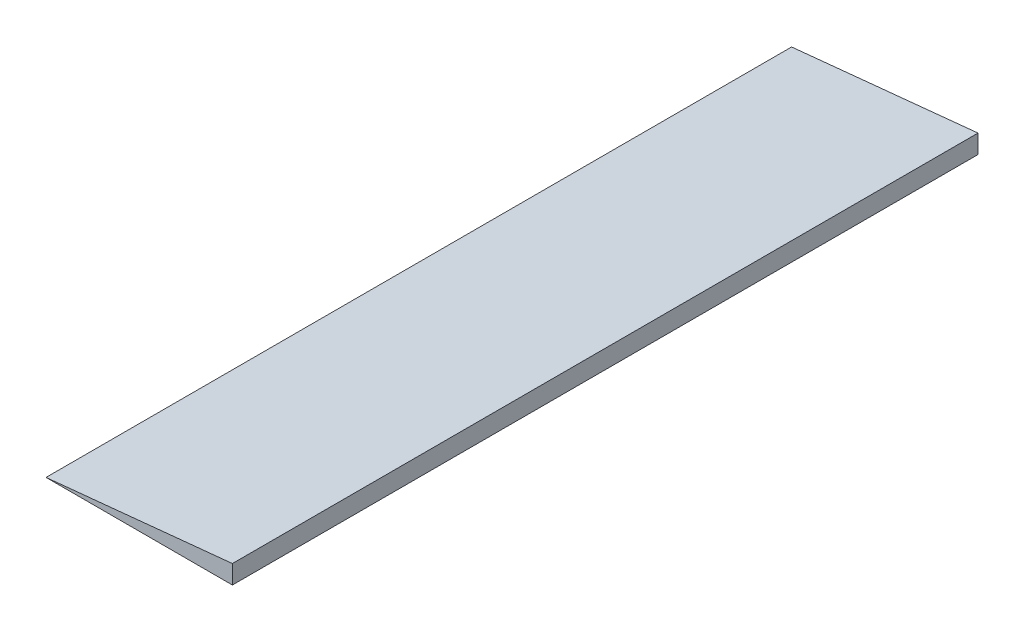
SolidWorks part; units mm, degrees
ref_plane "Front Plane" through (0, 0, 0) normal (0, 0, 1) x (1, 0, 0)
ref_plane "Top Plane" through (0, 0, 0) normal (0, 1, 0) x (1, 0, 0)
ref_plane "Right Plane" through (0, 0, 0) normal (1, 0, 0) x (0, 0, -1)
sketch "Sketch1" plane through (0, 0, 0) normal (0, 1, 0) x (1, 0, 0)
  line L1 (0, 0) -> (1000, 0)
  line L2 (0, 0) -> (0, 4000)
  line L3 (0, 4000) -> (1000, 4000)
  line L4 (1000, 0) -> (1000, 4000)
extrude "Boss-Extrude1" add sketch "Sketch1" along normal blind 100
sketch "Sketch2" plane through (0, 0, 0) normal (0, 0, 1) x (1, 0, 0)
  line L0 (0, 0) -> (1000, 100)
  line L1 (1000, 100) -> (0, 100)
  line L2 (0, 100) -> (0, 0)
extrude "Cut-Extrude1" cut sketch "Sketch2" against normal blind 5046
